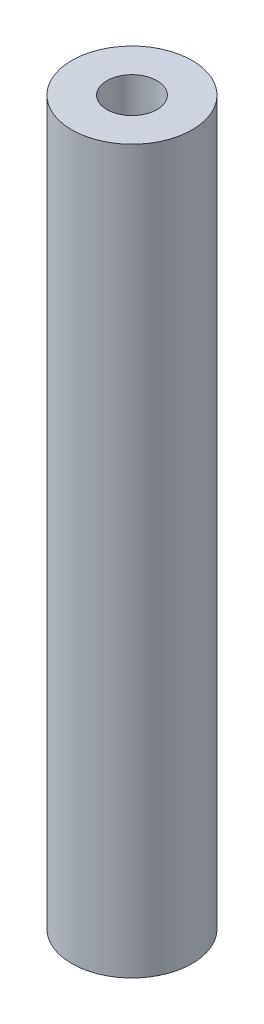
SolidWorks part; units mm, degrees
ref_plane "Front Plane" through (0, 0, 0) normal (0, 0, 1) x (1, 0, 0)
ref_plane "Top Plane" through (0, 0, 0) normal (0, 1, 0) x (1, 0, 0)
ref_plane "Right Plane" through (0, 0, 0) normal (1, 0, 0) x (0, 0, -1)
sketch "Sketch1" plane through (0, 0, 0) normal (0, 1, 0) x (1, 0, 0)
  circle A0 centre (0, 0) radius 3
  dimension "D1" = 6
extrude "Boss-Extrude1" add sketch "Sketch1" along normal blind 36
hole_wizard "Tap Drill for M3 Tap1" positions "Sketch3" profile "Sketch2" hole size "M3" standard "ISO"
sketch "Sketch3" plane through (0, 36, 0) normal (0, 1, 0) x (1, 0, 0)
  point P0 (0, 0)
sketch "Sketch2" plane through (0, 36, 0) normal (1, 0, 0) x (0, 0, 1)
  line L0 (0, 0) -> (0, 10.7511)
  line L1 (0, 10.7511) -> (1.25, 10)
  line L2 (1.25, 10) -> (1.25, 0)
  line L5 (1.25, 0) -> (0, 0)
  line L10 (0, 10.7511) -> (-1.25, 10) construction
  line L11 (0, -6.35) -> (0, 107.95) construction
  dimension "Hole Dia." = 2.5
  dimension "Hole Depth" = 10
  dimension "Drill Angle" = 118
hole_wizard "Tap Drill for M3 Tap2" positions "Sketch5" profile "Sketch4" hole size "M3" standard "ISO"
sketch "Sketch5" plane through (0, 0, 0) normal (0, -1, 0) x (-1, 0, 0)
  point P0 (0, 0)
sketch "Sketch4" plane through (0, 0, 0) normal (1, 0, 0) x (0, 0, -1)
  line L0 (0, 0) -> (0, 10.7511)
  line L1 (0, 10.7511) -> (1.25, 10)
  line L2 (1.25, 10) -> (1.25, 0)
  line L5 (1.25, 0) -> (0, 0)
  line L10 (0, 10.7511) -> (-1.25, 10) construction
  line L11 (0, -6.35) -> (0, 107.95) construction
  dimension "Hole Dia." = 2.5
  dimension "Hole Depth" = 10
  dimension "Drill Angle" = 118
